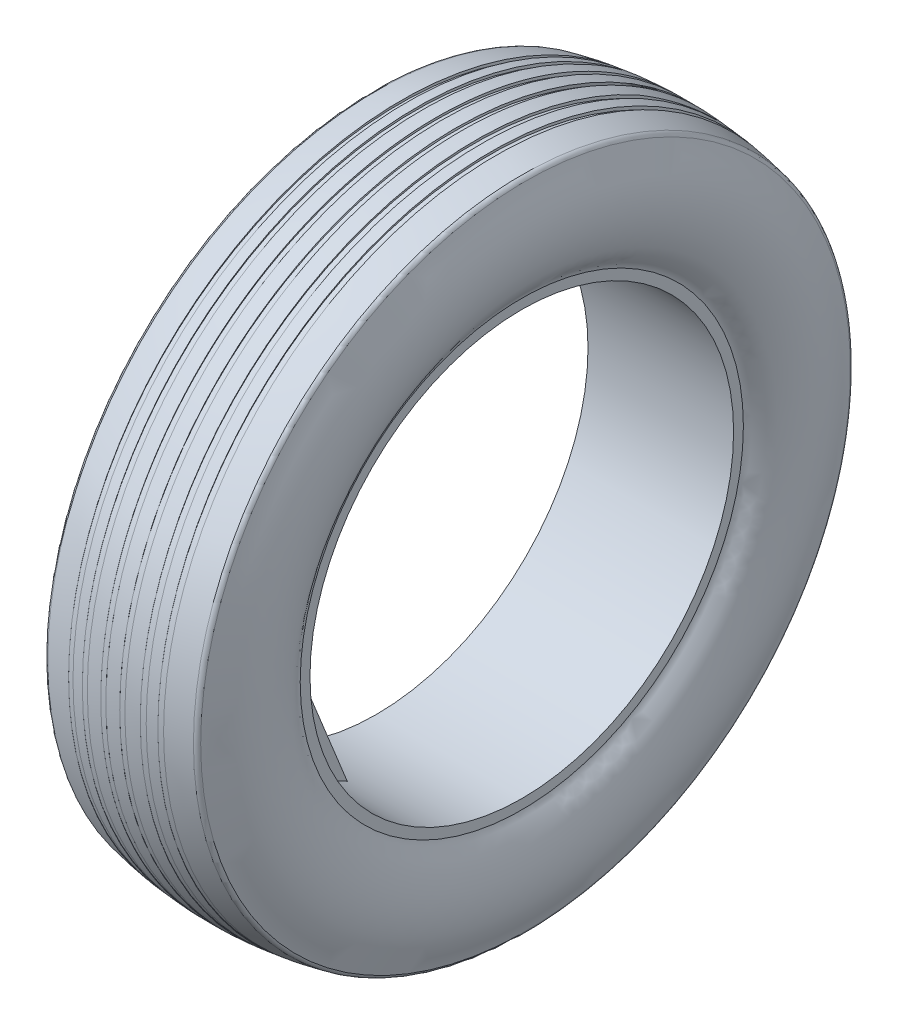
SolidWorks part; units mm, degrees
ref_plane "Front Plane" through (0, 0, 0) normal (0, 0, 1) x (1, 0, 0)
ref_plane "Top Plane" through (0, 0, 0) normal (0, 1, 0) x (1, 0, 0)
ref_plane "Right Plane" through (0, 0, 0) normal (1, 0, 0) x (0, 0, -1)
sketch "Sketch1" plane through (0, 0, 0) normal (0, 0, 1) x (1, 0, 0)
  line L0 (-7.9201, 256.54) -> (166.6701, 256.54)
  line L3 (166.6701, 256.54) -> (166.6701, 268.2701)
  line L6 (-7.9201, 268.2701) -> (-7.9201, 256.54)
  line L9 (79.375, 2.54) -> (144.0186, 2.54)
  arc A0 (171.1579, 392.0942) -> (166.248, 396.4191) centre (165.1056, 390.1727) ccw
  arc A1 (-12.4079, 392.0942) -> (-7.498, 396.4191) centre (-6.3556, 390.1727) cw
  arc A2 (166.6701, 396.327) -> (-7.9201, 396.327) centre (79.375, -2.5813) ccw
  spline S0 degree 3 poles (166.6701, 268.2701) (168.0269, 273.9331) (176.0523, 280.8768) (189.3298, 311.6291) (190.4573, 348.9301) (176.1599, 378.9422) (172.3319, 388.3963) (171.1579, 392.0942) knots 0 0 0 0 0.1243 0.226723 0.7391 0.879849 0.966039 0.966039 0.966039 0.966039
  spline S1 degree 3 poles (-7.9201, 268.2701) (-9.2769, 273.9331) (-17.3023, 280.8768) (-30.5798, 311.6291) (-31.7073, 348.9301) (-17.4099, 378.9422) (-13.5819, 388.3963) (-12.4079, 392.0942) knots 0 0 0 0 0.1243 0.226723 0.7391 0.879849 0.966039 0.966039 0.966039 0.966039
  dimension "D1" = 6.35
  dimension "D2" = 174.5902
revolve "Revolve4" add sketch "Sketch1" angle 360 about L9
ref_plane "Plane6" through (0, 0, 2.54) normal (0, 0, 1) x (1, 0, 0)
sketch "Sketch4" plane through (0, 0, 2.54) normal (0, 0, 1) x (1, 0, 0)
  line L0 (-29.207, 2.54) -> (187.957, 2.54)
  line L1 (47.625, 405.7669) -> (47.625, 401.9829)
  line L3 (41.0724, 401.4152) -> (41.0724, 405.7669)
  line L4 (41.0724, 405.7669) -> (47.625, 405.7669)
  line L5 (28.5004, 405.7669) -> (28.5004, 400.0253)
  line L7 (22.4145, 399.2094) -> (22.4145, 405.7669)
  line L8 (22.4145, 405.7669) -> (28.5004, 405.7669)
  line L9 (71.0838, 403.1422) -> (71.0838, 407.9578)
  line L10 (71.0838, 407.9578) -> (64.8755, 407.9578)
  line L11 (64.8755, 407.9578) -> (64.8755, 402.9678)
  line L12 (93.8745, 407.9578) -> (93.8745, 402.9678)
  line L13 (87.6662, 407.9578) -> (93.8745, 407.9578)
  line L14 (87.6662, 403.1422) -> (87.6662, 407.9578)
  line L15 (136.3355, 405.7669) -> (130.2496, 405.7669)
  line L16 (136.3355, 399.2094) -> (136.3355, 405.7669)
  line L17 (130.2496, 405.7669) -> (130.2496, 400.0253)
  line L18 (117.6776, 405.7669) -> (111.125, 405.7669)
  line L19 (117.6776, 401.4152) -> (117.6776, 405.7669)
  line L20 (111.125, 405.7669) -> (111.125, 401.9829)
  line L21 (-29.207, 331.2756) -> (-29.207, -326.1956) construction
  line L22 (187.957, -326.1956) -> (187.957, 331.2756) construction
  arc A0 (117.6776, 401.4152) -> (111.125, 401.9829) centre (79.375, -2.5813) ccw
  arc A1 (22.4145, 399.2094) -> (28.5004, 400.0253) centre (79.375, -2.5813) cw
  arc A2 (93.8745, 402.9678) -> (87.6662, 403.1422) centre (79.375, -2.5813) ccw
  arc A3 (64.8755, 402.9678) -> (71.0838, 403.1422) centre (79.375, -2.5813) cw
  arc A4 (136.3355, 399.2094) -> (130.2496, 400.0253) centre (79.375, -2.5813) ccw
  arc A5 (41.0724, 401.4152) -> (47.625, 401.9829) centre (79.375, -2.5813) cw
revolve "Cut-Revolve3" cut sketch "Sketch4" angle 360 about L0
